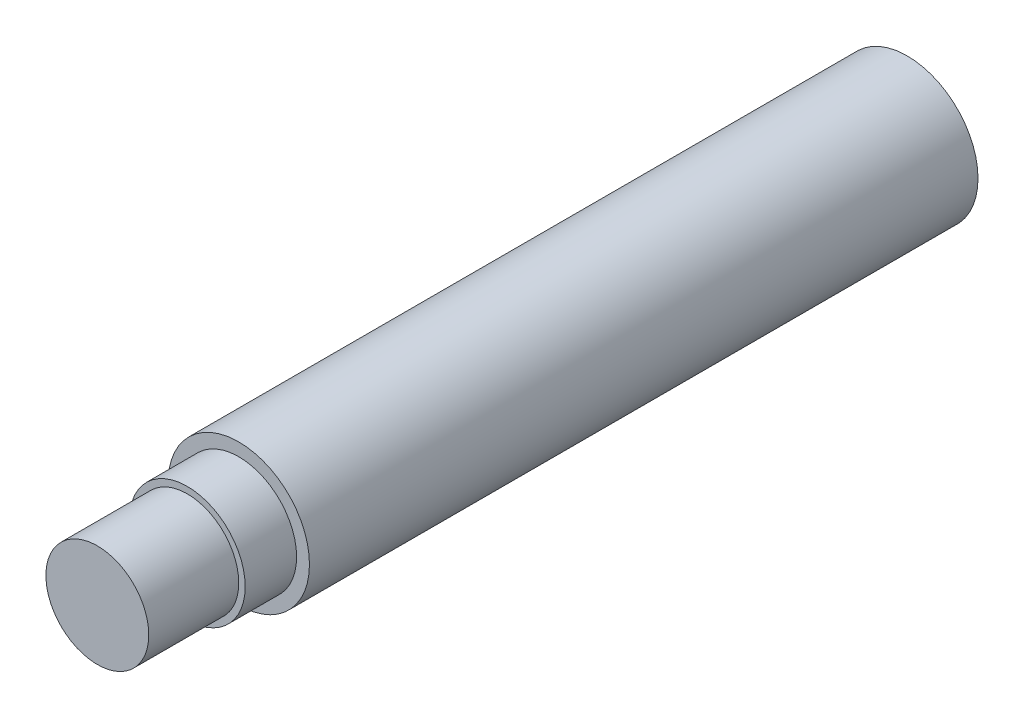
SolidWorks part; units mm, degrees
ref_plane "Front Plane" through (0, 0, 0) normal (0, 0, 1) x (1, 0, 0)
ref_plane "Top Plane" through (0, 0, 0) normal (0, 1, 0) x (1, 0, 0)
ref_plane "Right Plane" through (0, 0, 0) normal (1, 0, 0) x (0, 0, -1)
sketch "Sketch1" plane through (0, 0, 0) normal (0, 0, 1) x (1, 0, 0)
  circle A0 centre (0, 0) radius 5.5
  dimension "D1" = 11
extrude "Boss-Extrude1" add sketch "Sketch1" along normal blind 52
sketch "Sketch2" plane through (0, 0, 52) normal (0, 0, 1) x (1, 0, 0)
  circle A0 centre (0, 0) radius 4.5
  dimension "D1" = 9
extrude "Boss-Extrude2" add sketch "Sketch2" along normal blind 4
sketch "Sketch3" plane through (0, 0, 56) normal (0, 0, 1) x (1, 0, 0)
  circle A0 centre (0, 0) radius 4
  dimension "D1" = 8
extrude "Boss-Extrude3" add sketch "Sketch3" along normal blind 7
cosmetic thread "Cosmetic Thread1" parameters "D1"=7, "D2"=7
hole_wizard "Ø5.0 (5) Diameter Hole1" positions "Sketch6" profile "Sketch5" hole size "Ø5.0" standard "ANSI Metric"
sketch "Sketch6" plane through (0, 0, 0) normal (0, 0, -1) x (-1, 0, 0)
  point P0 (0, 0)
sketch "Sketch5" plane through (0, 0, 0) normal (1, 0, 0) x (0, 1, 0)
  line L0 (0, 0) -> (0, 46.5022)
  line L1 (0, 46.5022) -> (2.5, 45)
  line L2 (2.5, 45) -> (2.5, 0)
  line L5 (2.5, 0) -> (0, 0)
  line L10 (0, 46.5022) -> (-2.5, 45) construction
  line L11 (0, -6.35) -> (0, 107.95) construction
  dimension "Hole Dia." = 5
  dimension "Hole Depth" = 45
  dimension "Drill Angle" = 118
hole_wizard "M8x1.0 Tapped Hole1" positions "Sketch8" profile "Sketch7" tap size "M8x1.0" standard "ANSI Metric"
sketch "Sketch8" plane through (0, 0, 0) normal (0, 0, -1) x (-1, 0, 0)
  point P0 (0, 0)
sketch "Sketch7" plane through (0, 0, 0) normal (1, 0, 0) x (0, 1, 0)
  line L0 (0, 0) -> (0, 8.103)
  line L1 (0, 8.103) -> (3.5, 6)
  line L2 (3.5, 6) -> (3.5, 0.525)
  line L3 (3.5, 0.525) -> (4.025, 0)
  line L5 (4.025, 0) -> (0, 0)
  line L6 (-3.5, 0.525) -> (-4.025, 0) construction
  line L10 (0, 8.103) -> (-3.5, 6) construction
  line L11 (0, -6.35) -> (0, 107.95) construction
  dimension "Tap Drill Dia." = 7
  dimension "Tap Drill Depth" = 6
  dimension "Near C'Sink Dia." = 8.05
  dimension "Near C'Sink Angle" = 90
  dimension "Drill Angle" = 118
cosmetic thread "Hole Thread1" parameters "D1"=6, "D2"=8
